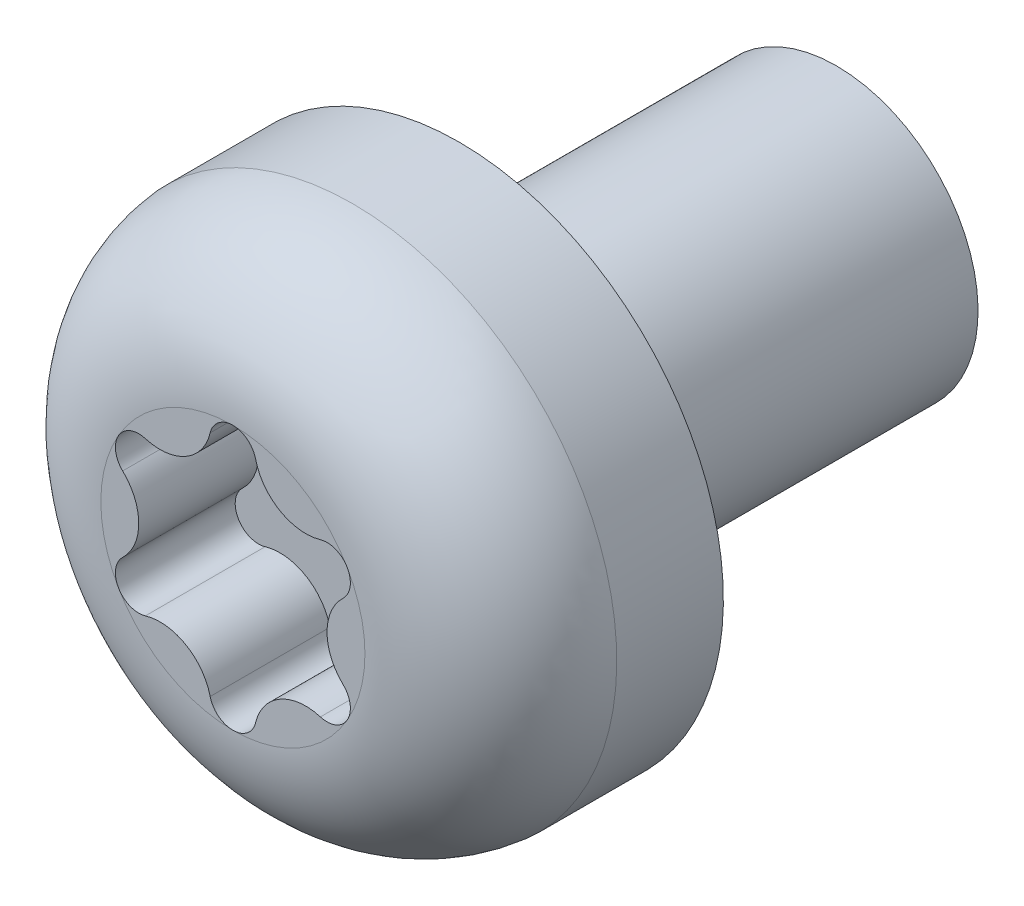
SolidWorks part; units mm, degrees
material "AISI Acier à outil type A2"
ref_plane "Face" through (0, 0, 0) normal (0, 0, 1) x (1, 0, 0)
ref_plane "Dessus" through (0, 0, 0) normal (0, 1, 0) x (1, 0, 0)
ref_plane "Droite" through (0, 0, 0) normal (1, 0, 0) x (0, 0, -1)
sketch "Esquisse1" plane through (0, 0, 0) normal (1, 0, 0) x (0, 0, -1)
  line L0 (-2.4, 0) -> (-2.4, 1.4)
  line L1 (-1.13, 2.8) -> (0, 2.8)
  line L2 (0, 2.8) -> (0, 1.5)
  line L3 (0, 1.5) -> (4, 1.5)
  line L4 (4, 1.5) -> (4, 0)
  line L5 (4, 0) -> (-2.4, 0)
  line L6 (-2.4, 0) -> (-4.3313, 0) construction
  arc A0 (-2.4, 1.4) -> (-1.13, 2.8) centre (-0.9933, 1.4) cw
  dimension "L" = 4
  dimension "K" = 2.4
  dimension "T" = 1.27
  dimension "M" = 3
  dimension "DH" = 5.6
  dimension "A" = 2.8
revolve "Révolution1" add sketch "Esquisse1" angle 360 about L6
cosmetic thread "Représentation de filetage1" parameters "D2"=2.3866
sketch "Esquisse2" plane through (0, 0, 2.4) normal (0, 0, 1) x (1, 0, 0)
  line L0 (0, -1.0692) -> (0, 1.0844) construction
  line L1 (0, 0) -> (-0.1844, 0.9269) construction
  line L2 (0, 0) -> (0.1807, 0.9086) construction
  line L3 (0, 0) -> (0.8195, 0.4731) construction
  line L4 (0, 0) -> (0.7063, 0.6194) construction
  line L5 (0, 0) -> (0.3928, 0.6804) construction
  line L7 (0, 1.1524) -> (-0.998, 0.5762) construction
  line L8 (-0.998, 0.5762) -> (-0.998, -0.5762) construction
  line L9 (-0.998, -0.5762) -> (0, -1.1524) construction
  line L10 (0, -1.1524) -> (0.998, -0.5762) construction
  line L11 (0.998, -0.5762) -> (0.998, 0.5762) construction
  line L12 (0.998, 0.5762) -> (0, 1.1524) construction
  circle A0 centre (0, 0) radius 1.4 construction
  circle A1 centre (0, 0) radius 1.4 construction
  arc A2 (-0.2407, 1.2102) -> (0.2407, 1.2102) centre (0, 1.1524) cw
  circle A3 centre (0, 0) radius 0.998 construction
  arc A4 (0.2407, 1.2102) -> (0.9277, 0.8136) centre (0.7724, 1.3379) ccw
  arc A5 (0.9277, 0.8136) -> (1.1684, 0.3966) centre (0.998, 0.5762) cw
  arc A6 (1.1684, 0.3966) -> (1.1684, -0.3966) centre (1.5448, 0) ccw
  arc A7 (1.1684, -0.3966) -> (0.9277, -0.8136) centre (0.998, -0.5762) cw
  arc A8 (0.9277, -0.8136) -> (0.2407, -1.2102) centre (0.7724, -1.3379) ccw
  arc A9 (0.2407, -1.2102) -> (-0.2407, -1.2102) centre (0, -1.1524) cw
  arc A10 (-0.2407, -1.2102) -> (-0.9277, -0.8136) centre (-0.7724, -1.3379) ccw
  arc A11 (-0.9277, -0.8136) -> (-1.1684, -0.3966) centre (-0.998, -0.5762) cw
  arc A12 (-1.1684, -0.3966) -> (-1.1684, 0.3966) centre (-1.5448, 0) ccw
  arc A13 (-1.1684, 0.3966) -> (-0.9277, 0.8136) centre (-0.998, 0.5762) cw
  arc A14 (-0.9277, 0.8136) -> (-0.2407, 1.2102) centre (-0.7724, 1.3379) ccw
  point P22 (0.499, 0.8643)
  dimension "D1" = 22.5
  dimension "D2" = 60
  dimension "D3" = 11.25
  dimension "D4" = 6
extrude "Enlèv. mat.-Extru.1" cut sketch "Esquisse2" against normal blind 1.27
equation "\"D3@Esquisse2\" = \"D1@Esquisse2\"/2"
equation "\"D1@Enlèv. mat.-Extru.1\" = \"T@Esquisse1\""
